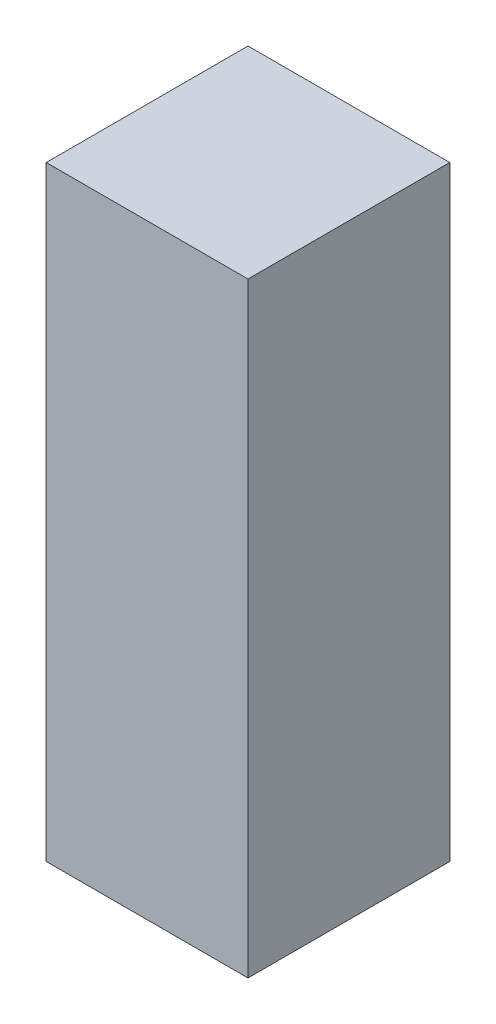
SolidWorks part; units mm, degrees
ref_plane "Front Plane" through (0, 0, 0) normal (0, 0, 1) x (1, 0, 0)
ref_plane "Top Plane" through (0, 0, 0) normal (0, 1, 0) x (1, 0, 0)
ref_plane "Right Plane" through (0, 0, 0) normal (1, 0, 0) x (0, 0, -1)
sketch "Sketch1" plane through (0, 0, 0) normal (0, 1, 0) x (1, 0, 0)
  line L1 (-52.7987, 32.2514) -> (-2.7987, 32.2514)
  line L2 (-52.7987, 32.2514) -> (-52.7987, -17.7486)
  line L3 (-52.7987, -17.7486) -> (-2.7987, -17.7486)
  line L4 (-2.7987, 32.2514) -> (-2.7987, -17.7486)
  dimension "D1" = 50
  dimension "D2" = 50
extrude "Boss-Extrude1" add sketch "Sketch1" along normal blind 150
sketch "Sketch2" plane through (0, 0, 0) normal (0, -1, 0) x (1, 0, 0)
  line L1 (-2.7987, 17.7486) -> (-2.7987, -32.2514) construction
  line L2 (-52.7987, 17.7486) -> (-2.7987, 17.7486) construction
  circle A0 centre (-27.7987, -7.2514) radius 15
  point P2 (-26.7279, -8.3892)
  point P7 (0, 0)
  dimension "D1" = 25
  dimension "D2" = 25
extrude "Cut-Extrude1" cut sketch "Sketch2" against normal blind 100 contours A0
